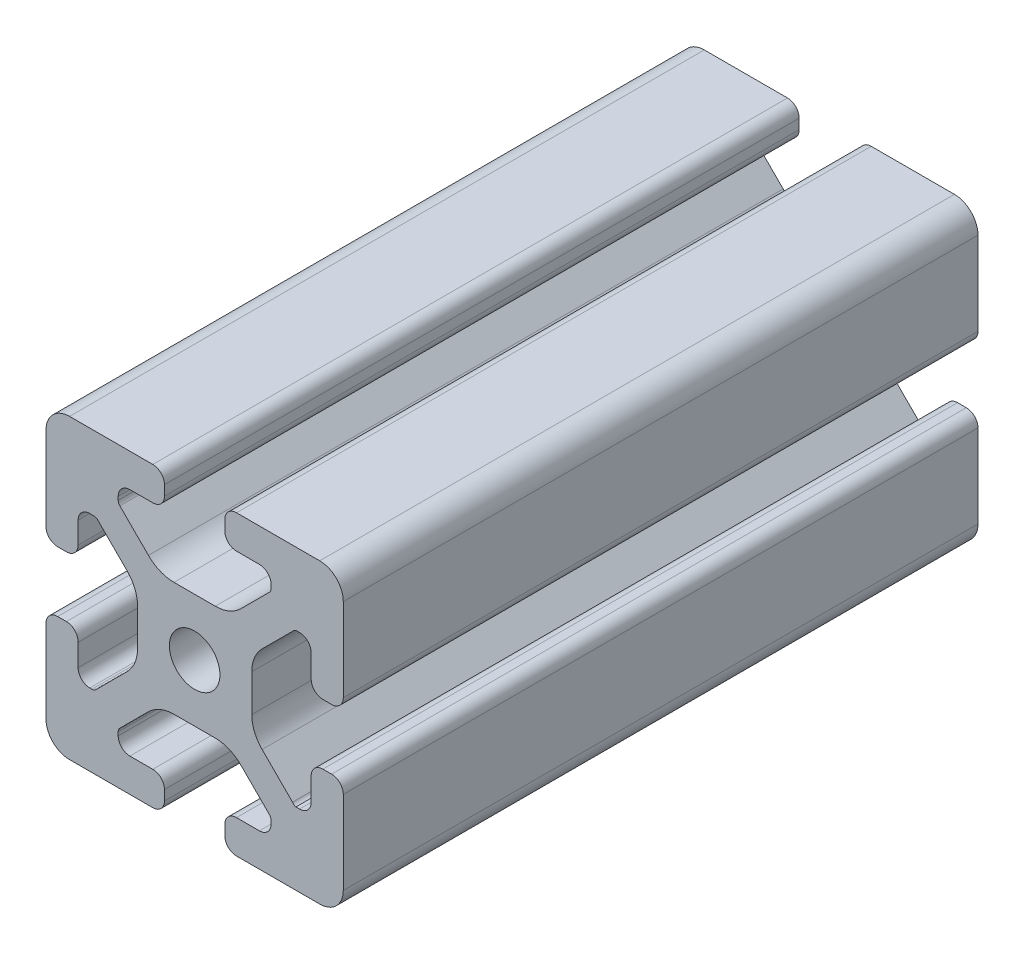
SolidWorks part; units mm, degrees
material "6105-T5 Aluminum"
ref_plane "Front Plane" through (0, 0, 0) normal (0, 0, 1) x (1, 0, 0)
ref_plane "Top Plane" through (0, 0, 0) normal (0, 1, 0) x (1, 0, 0)
ref_plane "Right Plane" through (0, 0, 0) normal (1, 0, 0) x (0, 0, -1)
sketch "Sketch1" plane through (0, 0, 0) normal (0, 0, 1) x (1, 0, 0)
  line L0 (0, 19.7407) -> (0, -19.7407) construction
  line L1 (19.0335, 0) -> (-20.7246, 0) construction
  line L2 (-8.715, -15.5246) -> (-5.63, -15.5246)
  line L3 (-10.285, -13.9546) -> (-10.285, -13.4925)
  line L4 (-6.2171, -9.1098) -> (-10.0624, -12.9551)
  line L5 (2.7773, -7.685) -> (-2.7773, -7.685)
  line L6 (10.0624, -12.9551) -> (6.2171, -9.1098)
  line L7 (10.285, -13.9546) -> (10.285, -13.4925)
  line L8 (5.63, -15.5246) -> (8.715, -15.5246)
  line L9 (4.06, -18.43) -> (4.06, -17.0946)
  line L10 (-4.06, -18.43) -> (-4.06, -17.0946)
  line L11 (15.68, -8.7154) -> (15.68, -5.63)
  line L12 (-14.11, -10.2854) -> (-13.8169, -10.2854)
  line L13 (20, -16.83) -> (20, -5.63)
  line L14 (20, 5.63) -> (20, 13.0011)
  line L15 (-16.83, 20) -> (-5.63, 20)
  line L16 (5.63, 20) -> (12.9796, 20)
  line L18 (-8.715, 15.5246) -> (-5.63, 15.5246)
  line L19 (-20, -17.0184) -> (-20, -5.7579)
  line L20 (-20, 5.573) -> (-20, 13.0045)
  line L21 (-15.68, -8.7154) -> (-15.68, -5.7579)
  line L23 (-16.6746, -20) -> (-5.63, -20)
  line L24 (5.63, -20) -> (13, -20)
  line L53 (14.11, -10.2854) -> (13.6201, -10.2854)
  line L54 (13.1637, -9.947) -> (9.0762, -5.8595)
  line L55 (7.685, -2.5008) -> (7.685, 2.5008)
  line L56 (9.0762, 5.8595) -> (13.2795, 10.0628)
  line L57 (13.8169, 10.2854) -> (14.11, 10.2854)
  line L58 (15.68, 8.7154) -> (15.68, 5.63)
  line L59 (17.25, 4.06) -> (18.43, 4.06)
  line L61 (20, 13.0011) -> (20, 16.83)
  line L62 (16.83, 20) -> (12.9796, 20)
  line L64 (4.06, 18.43) -> (4.06, 17.0946)
  line L65 (5.63, 15.5246) -> (8.715, 15.5246)
  line L66 (10.285, 13.9546) -> (10.285, 13.4925)
  line L67 (10.0624, 12.9551) -> (6.2171, 9.1098)
  line L68 (2.7773, 7.685) -> (-2.7773, 7.685)
  line L69 (-6.2171, 9.1098) -> (-10.0624, 12.9551)
  line L70 (-10.285, 13.4925) -> (-10.285, 13.9546)
  line L72 (-4.06, 17.0946) -> (-4.06, 18.43)
  line L75 (-20, 16.83) -> (-20, 13.0045)
  line L77 (-18.43, 4.003) -> (-17.25, 4.003)
  line L78 (-15.68, 5.573) -> (-15.68, 8.4757)
  line L79 (-14.0552, 10.0447) -> (-13.7199, 10.033)
  line L80 (-13.0405, 9.8238) -> (-9.0762, 5.8595)
  line L81 (-7.685, 2.5008) -> (-7.685, -2.5008)
  line L82 (-9.0762, -5.8595) -> (-13.2795, -10.0628)
  line L85 (-17.25, -4.1204) -> (-18.43, -4.1204)
  line L100 (13, -20) -> (16.83, -20)
  line L103 (18.43, -4.06) -> (17.25, -4.06)
  arc A0 (-5.63, -15.5246) -> (-4.06, -17.0946) centre (-5.63, -17.0946) cw
  arc A1 (-8.715, -15.5246) -> (-10.285, -13.9546) centre (-8.715, -13.9546) cw
  arc A2 (-10.285, -13.4925) -> (-10.0624, -12.9551) centre (-9.525, -13.4925) cw
  arc A3 (-6.2171, -9.1098) -> (-2.7773, -7.685) centre (-2.7773, -12.5496) cw
  arc A4 (2.7773, -7.685) -> (6.2171, -9.1098) centre (2.7773, -12.5496) cw
  arc A5 (10.0624, -12.9551) -> (10.285, -13.4925) centre (9.525, -13.4925) cw
  arc A6 (10.285, -13.9546) -> (8.715, -15.5246) centre (8.715, -13.9546) cw
  arc A7 (4.06, -17.0946) -> (5.63, -15.5246) centre (5.63, -17.0946) cw
  arc A8 (5.63, -20) -> (4.06, -18.43) centre (5.63, -18.43) cw
  arc A9 (-4.06, -18.43) -> (-5.63, -20) centre (-5.63, -18.43) cw
  circle A45 centre (0, 0) radius 3.4
  arc A46 (17.25, -4.06) -> (15.68, -5.63) centre (17.25, -5.63) ccw
  arc A47 (14.11, -10.2854) -> (15.68, -8.7154) centre (14.11, -8.7154) ccw
  arc A48 (13.1637, -9.947) -> (13.6201, -10.2854) centre (13.8117, -9.55) ccw
  arc A49 (7.685, -2.5008) -> (9.0762, -5.8595) centre (12.435, -2.5008) ccw
  arc A50 (9.0762, 5.8595) -> (7.685, 2.5008) centre (12.435, 2.5008) ccw
  arc A51 (13.8169, 10.2854) -> (13.2795, 10.0628) centre (13.8169, 9.5254) ccw
  arc A52 (15.68, 8.7154) -> (14.11, 10.2854) centre (14.11, 8.7154) ccw
  arc A53 (15.68, 5.63) -> (17.25, 4.06) centre (17.25, 5.63) ccw
  arc A54 (18.43, 4.06) -> (20, 5.63) centre (18.43, 5.63) ccw
  arc A55 (20, 16.83) -> (16.83, 20) centre (16.83, 16.83) ccw
  arc A56 (5.63, 20) -> (4.06, 18.43) centre (5.63, 18.43) ccw
  arc A57 (4.06, 17.0946) -> (5.63, 15.5246) centre (5.63, 17.0946) ccw
  arc A58 (10.285, 13.9546) -> (8.715, 15.5246) centre (8.715, 13.9546) ccw
  arc A59 (10.0624, 12.9551) -> (10.285, 13.4925) centre (9.525, 13.4925) ccw
  arc A60 (2.7773, 7.685) -> (6.2171, 9.1098) centre (2.7773, 12.5496) ccw
  arc A61 (-6.2171, 9.1098) -> (-2.7773, 7.685) centre (-2.7773, 12.5496) ccw
  arc A62 (-10.285, 13.4925) -> (-10.0624, 12.9551) centre (-9.525, 13.4925) ccw
  arc A63 (-8.715, 15.5246) -> (-10.285, 13.9546) centre (-8.715, 13.9546) ccw
  arc A64 (-5.63, 15.5246) -> (-4.06, 17.0946) centre (-5.63, 17.0946) ccw
  arc A65 (-4.06, 18.43) -> (-5.63, 20) centre (-5.63, 18.43) ccw
  arc A66 (-16.83, 20) -> (-20, 16.83) centre (-16.83, 16.83) ccw
  arc A67 (-20, 5.573) -> (-18.43, 4.003) centre (-18.43, 5.573) ccw
  arc A68 (-17.25, 4.003) -> (-15.68, 5.573) centre (-17.25, 5.573) ccw
  arc A69 (-14.0552, 10.0447) -> (-15.68, 8.4757) centre (-14.11, 8.4757) ccw
  arc A70 (-13.0405, 9.8238) -> (-13.7199, 10.033) centre (-13.5779, 9.2864) ccw
  arc A71 (-7.685, 2.5008) -> (-9.0762, 5.8595) centre (-12.435, 2.5008) ccw
  arc A72 (-9.0762, -5.8595) -> (-7.685, -2.5008) centre (-12.435, -2.5008) ccw
  arc A73 (-13.8169, -10.2854) -> (-13.2795, -10.0628) centre (-13.8169, -9.5254) ccw
  arc A74 (-15.68, -8.7154) -> (-14.11, -10.2854) centre (-14.11, -8.7154) ccw
  arc A75 (-15.68, -5.7579) -> (-17.25, -4.1204) centre (-17.2485, -5.6904) ccw
  arc A76 (-18.43, -4.1204) -> (-20, -5.7579) centre (-18.4315, -5.6904) ccw
  arc A77 (-20, -17.0184) -> (-16.6746, -20) centre (-16.8354, -16.8341) ccw
  arc A88 (16.83, -20) -> (20, -16.83) centre (16.83, -16.83) ccw
  arc A89 (20, -5.63) -> (18.43, -4.06) centre (18.43, -5.63) ccw
  dimension "D2" = 6.8
  dimension "D7" = 20.57
  dimension "D1" = 40
  dimension "D3" = 4.32
  dimension "D4" = 15.37
  dimension "D5" = 20
  dimension "D6" = 4.32
  dimension "D9" = 15.37
extrude "Extrude1" add sketch "Sketch1" against normal blind 85.4
